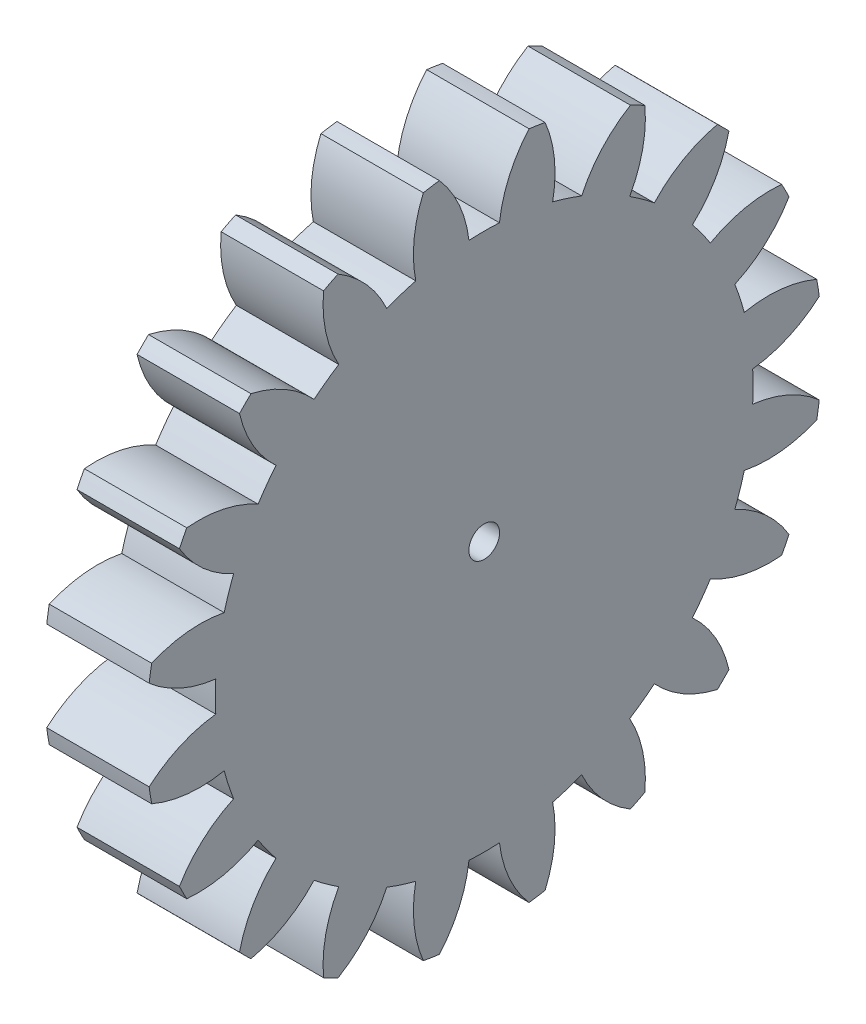
SolidWorks part; units mm, degrees
ref_plane "Plane1" through (0, 0, 0) normal (0, 0, 1) x (1, 0, 0)
ref_plane "Plane2" through (0, 0, 0) normal (0, 1, 0) x (1, 0, 0)
ref_plane "Plane3" through (0, 0, 0) normal (1, 0, 0) x (0, 0, -1)
sketch "HoldingSke" plane through (0, 0, 0) normal (0, 1, 0) x (1, 0, 0)
  line L0 (0, 0) -> (0.6265, -0.228)
  line L1 (-15, 0) -> (100, 0) construction
  line L2 (0, 0) -> (-2.1039, 2.3779)
  line L3 (0, 0) -> (-11.863, 4.5341)
  line L4 (0, 0) -> (8.1152, 2.9537)
  line L5 (0, 0) -> (-46.8476, -17.4728)
  line L6 (0, 0) -> (-4.1448, -2.7965)
  line L7 (-2.1039, 2.3779) -> (8.6586, 51.2059)
  line L8 (-76.2, 54.61) -> (-76, 54.61)
  line L9 (-71.009, 38.7566) -> (-53.1078, 45.2721)
  line L10 (-76.2, 71.12) -> (104.1128, 71.12)
  line L11 (0, 0) -> (-5, 0)
  line L12 (-76.2, 101.6) -> (-76.147, 101.6)
  line L13 (24.9733, 27.94) -> (52.9518, 28.4284)
  line L14 (24.9733, 27.94) -> (24.9743, 27.94)
  line L15 (24.9733, 27.94) -> (100.4006, 29.5858)
  line L16 (-63.627, -1.5) -> (-12.827, -1.5)
  circle A0 centre (0, 0) radius 0.75
  circle A1 centre (0, 0) radius 13.124
  circle A2 centre (0, 0) radius 37.5
  circle A3 centre (0, 0) radius 0.75
  dimension "MHD" = 26.248
  dimension "Hub_dia" = 75
  dimension "Bore" = 1.5
  dimension "MBD" = 1.5
  dimension "Num_teeth" = 20
  dimension "Pitch" = 0.6667
  dimension "Overall_len" = 50
  dimension "Show_teeth" = 20
  dimension "Thickness" = 5
  dimension "OAL" = 50.0001
  dimension "T_dim" = 0.2
  dimension "Ap" = 20
  dimension "H" = 19.05
  dimension "Pitch_radius" = 180.3128
  dimension "Width" = 5
  dimension "Backlash" = 0.053
  dimension "Addendum_fac" = 1
  dimension "Dedendum_fac" = 1.25
  dimension "Clearance_fac" = 0.25
  dimension "Dedendum_add" = 0.001
  dimension "Module" = 1.5
sketch "BasProSke" plane through (0, 0, 0) normal (0, 1, 0) x (1, 0, 0)
  line L0 (-10, 0) -> (60, 0) construction
  line L1 (0, 0) -> (0, 16.5)
  line L2 (0, 0) -> (5, 0)
  line L3 (5, 0) -> (5, 16.5)
  line L4 (5, 16.5) -> (0, 16.5)
  dimension "Thickness" = 5
  dimension "Diameter" = 33
revolve "Base-Revolve" add sketch "BasProSke" angle 360 about L0
sketch "TooCutSke" plane through (0, 0, 0) normal (1, 0, 0) x (0, 0, -1)
  line L1 (0, 0) -> (0, 107) construction
  line L2 (0, 0) -> (-1.2696, 14.9462) construction
  line L3 (0, 0) -> (-4.6808, 29.5532) construction
  line L4 (-1.2696, 14.9462) -> (-2.3404, 14.7766) construction
  arc A0 (0.7438, 13.1029) -> (-0.7438, 13.1029) centre (0, 0) ccw
  arc A1 (2.21, 16.377) -> (-2.21, 16.377) centre (0, 0) ccw
  circle A2 centre (0, 0) radius 15 construction
  circle A3 centre (0, 0) radius 14.0954 construction
  arc A4 (-0.7438, 13.1029) -> (-2.21, 16.377) centre (-6.7025, 12.3999) ccw
  arc A5 (2.21, 16.377) -> (0.7438, 13.1029) centre (6.7025, 12.3999) ccw
  dimension "Root_dia" = 26.248
  dimension "Overcut_dia" = 33.0508
  dimension "Pitch_dia" = 30
  dimension "Base_dia" = 28.1908
  dimension "Flank_rad" = 6
  dimension "Half_ang" = 9
  dimension "Half_CT" = 1.0841
extrude "ToothCut" cut sketch "TooCutSke" along normal through all
fillet "Breaks" [suppressed] radius 0.03
fillet "RootFillets" [suppressed] radius 0.376
pattern_circular "TeethCuts" count 20 every 18 about axis through (-10, 0, 0) along (1, 0, 0) of "ToothCut", "RootFillets", "Breaks"
sketch "HubNeaOneSke" plane through (0, 0, 0) normal (-1, 0, 0) x (0, 0, 1)
  circle A0 centre (0, 0) radius 13.124
  dimension "Diameter" = 26.248
extrude "HubNearOne" [suppressed] add sketch "HubNeaOneSke" along normal blind 45.0001
sketch "HubNeaBotSke" plane through (0, 0, 0) normal (-1, 0, 0) x (0, 0, 1)
  circle A0 centre (0, 0) radius 13.124
  dimension "Diameter" = 26.248
extrude "HubNearBoth" [suppressed] add sketch "HubNeaBotSke" along normal blind 22.5
ref_plane "FarPln" through (5, 0, 0) normal (1, 0, 0) x (0, 0, -1)
sketch "HubFarSke" plane through (5, 0, 0) normal (1, 0, 0) x (0, 0, -1)
  circle A0 centre (0, 0) radius 13.124
  dimension "Diameter" = 26.248
extrude "HubFar" [suppressed] add sketch "HubFarSke" along normal blind 22.5
sketch "BorSke" plane through (0, 0, 0) normal (1, 0, 0) x (0, 0, -1)
  circle A0 centre (0, 0) radius 0.75
  dimension "Diameter" = 1.5
extrude "Bore" cut sketch "BorSke" along normal mid plane 100.0001
sketch "KeySke" plane through (0, 0, 0) normal (1, 0, 0) x (0, 0, -1)
  line L0 (-0.3, 0) -> (-0.3, 0.95)
  line L1 (-0.3, 0.95) -> (0.3, 0.95)
  line L2 (0.3, 0.95) -> (0.3, 0)
  line L3 (0, 0) -> (0, 34) construction
  line L4 (-0.3, 0) -> (0.3, 0)
  dimension "Offset" = 0.95
  dimension "Width" = 0.6
extrude "Keyway" [suppressed] cut sketch "KeySke" along normal mid plane 100.0001
pattern_circular "Keyway2" [suppressed] count 2 every 90 about axis through (-10, 0, 0) along (1, 0, 0)
equation "' \"Module@HoldingSke\" = 6.35"
equation "' \"Num_teeth@HoldingSke\" = 12"
equation "' \"Ap@HoldingSke\" =  20"
equation "' \"Ap@HoldingSke\" = 20"
equation "' \"Width@HoldingSke\" = 0.5 * 25.4"
equation "' \"Hub_dia@HoldingSke\"= 1 * 25.4"
equation "' \"Hub_dia@HoldingSke\" = 1 * 25.4"
equation "' \"Overall_len@HoldingSke\" = 1.0 * 25.4"
equation "' \"Bore@HoldingSke\" = 0.75 * 25.4"
equation "' \"T_dim@HoldingSke\" = 0.1 * 25.4"
equation "' \"Width@KeySke\" = 0.25 * 25.4"
equation "' \"Show_teeth@HoldingSke\" = 13"
equation "' \"Backlash@HoldingSke\" = 0.009 * 25.4"
equation "' \"Addendum_fac@HoldingSke\" = 1.0"
equation "' \"Dedendum_fac@HoldingSke\" = 1.25"
equation "' \"Dedendum_add@HoldingSke\" = 0.00005 * 25.4"
equation "' \"Clearance_fac@HoldingSke\" = 0.25"
equation "\"Pitch@HoldingSke\" = 1 / \"Module@HoldingSke\""
equation "\"Overcut_dia@TooCutSke\" = (\"Num_teeth@HoldingSke\" + 2 * \"Addendum_fac@HoldingSke\") / \"Pitch@HoldingSke\" + 0.002 * 25.4"
equation "\"Pitch_dia@TooCutSke\" = \"Num_teeth@HoldingSke\" / \"Pitch@HoldingSke\""
equation "\"Base_dia@TooCutSke\" = \"Num_teeth@HoldingSke\" / \"Pitch@HoldingSke\" * cos((\"Ap@HoldingSke\"  * 3.14159265 / 180))"
equation "\"Root_dia@TooCutSke\" = (\"Num_teeth@HoldingSke\" + 2) / \"Pitch@HoldingSke\" - 2 * (\"Addendum_fac@HoldingSke\" + \"Dedendum_fac@HoldingSke\") / \"Pitch@HoldingSke\" - \"Dedendum_add@HoldingSke\" * 2"
equation "\"Half_ang@TooCutSke\" = 180 / \"Num_teeth@HoldingSke\""
equation "\"Half_CT@TooCutSke\" = \"Num_teeth@HoldingSke\" / \"Pitch@HoldingSke\" * sin((3.14159265 / 2 / \"Num_teeth@HoldingSke\")) / 2 - 7 * \"Backlash@HoldingSke\" / 4"
equation "\"Flank_rad@TooCutSke\" = \"Num_teeth@HoldingSke\" / \"Pitch@HoldingSke\" / 5"
equation "\"Radius@RootFillets\" = \"Clearance_fac@HoldingSke\" / \"Pitch@HoldingSke\" + \"Dedendum_add@HoldingSke\""
equation "\"Break_rad@Breaks\" = 0.02 / \"Pitch@HoldingSke\""
equation "\"Thickness@HoldingSke\" = \"Width@HoldingSke\""
equation "\"OAL@HoldingSke\" = \"Thickness@HoldingSke\""
equation "\"MHD@HoldingSke\" = (\"Num_teeth@HoldingSke\" + 2) / \"Pitch@HoldingSke\" - 2 * (\"Addendum_fac@HoldingSke\" + \"Dedendum_fac@HoldingSke\")  / \"Pitch@HoldingSke\" - \"Dedendum_add@HoldingSke\" * 2"
equation "\"MBD@HoldingSke\" = (\"Num_teeth@HoldingSke\" + 2) / \"Pitch@HoldingSke\" - 2 * (\"Addendum_fac@HoldingSke\" + \"Dedendum_fac@HoldingSke\")  / \"Pitch@HoldingSke\" - \"Dedendum_add@HoldingSke\" * 2 - 0.002 * 25.4"
equation "\"MHD@HoldingSke\" = ((sgn( \"MHD@HoldingSke\" - \"Hub_dia@HoldingSke\" )-1)*( \"MHD@HoldingSke\" - \"Hub_dia@HoldingSke\" ))/-2+ \"Hub_dia@HoldingSke\""
equation "\"MBD@HoldingSke\" = ((sgn( \"MBD@HoldingSke\" - \"Bore@HoldingSke\" )-1)*( \"MBD@HoldingSke\" - \"Bore@HoldingSke\" ))/-2+ \"Bore@HoldingSke\""
equation "\"OAL@HoldingSke\" = ((sgn( \"OAL@HoldingSke\" - \"Overall_len@HoldingSke\" )+1)*( \"OAL@HoldingSke\" - \"Overall_len@HoldingSke\" ))/2 + \"Overall_len@HoldingSke\" + 0.000002 * 25.4"
equation "\"Num_teeth@TeethCuts\" = int( \"Show_teeth@HoldingSke\" ) + 1"
equation "\"Num_teeth@TeethCuts\" = ((sgn( \"Num_teeth@TeethCuts\" - \"Num_teeth@HoldingSke\" )-1)*( \"Num_teeth@TeethCuts\" - \"Num_teeth@HoldingSke\" ))/-2+ \"Num_teeth@HoldingSke\""
equation "\"Num_teeth@TeethCuts\" = ((sgn( \"Num_teeth@TeethCuts\" - 2.0)+1)*( \"Num_teeth@TeethCuts\" - 2.0))/2 +2.0"
equation "\"Angle@TeethCuts\" = 360.0 / \"Num_teeth@HoldingSke\""
equation "\"Diameter@BasProSke\" = (\"Num_teeth@HoldingSke\" + 2 * \"Addendum_fac@HoldingSke\") / \"Pitch@HoldingSke\""
equation "\"Thickness@BasProSke\"  = \"Thickness@HoldingSke\""
equation "' \"Fillet_rad@BasProSke\" =  \"Thickness@HoldingSke\" * 0.05"
equation "' \"Fillet_rad@BasProSke\" = \"Thickness@HoldingSke\" * 0.05"
equation "\"MHD@HoldingSke\" = ((sgn( \"MHD@HoldingSke\" - \"Root_dia@TooCutSke\" )-1)*( \"MHD@HoldingSke\" - \"Root_dia@TooCutSke\" ))/-2+ \"Root_dia@TooCutSke\""
equation "\"Diameter@HubNeaOneSke\" = \"MHD@HoldingSke\""
equation "\"Length@HubNearOne\" = \"OAL@HoldingSke\" - \"Thickness@BasProSke\""
equation "\"Diameter@HubNeaBotSke\" = \"MHD@HoldingSke\""
equation "\"Length@HubNearBoth\" = ( \"OAL@HoldingSke\" - \"Thickness@BasProSke\" ) / 2.0"
equation "\"Thickness@FarPln\" = \"Thickness@BasProSke\""
equation "\"Diameter@HubFarSke\" = \"MHD@HoldingSke\""
equation "\"Length@HubFar\" = ( \"OAL@HoldingSke\" - \"Thickness@BasProSke\" ) / 2.0"
equation "\"Diameter@BorSke\" = \"MBD@HoldingSke\""
equation "\"D1@Bore\" = \"OAL@HoldingSke\" * 2.0"
equation "\"D1@Keyway\" = \"OAL@HoldingSke\" * 2.0"
equation "\"Offset@KeySke\" = \"T_dim@HoldingSke\" + \"MBD@HoldingSke\" / 2.0"
